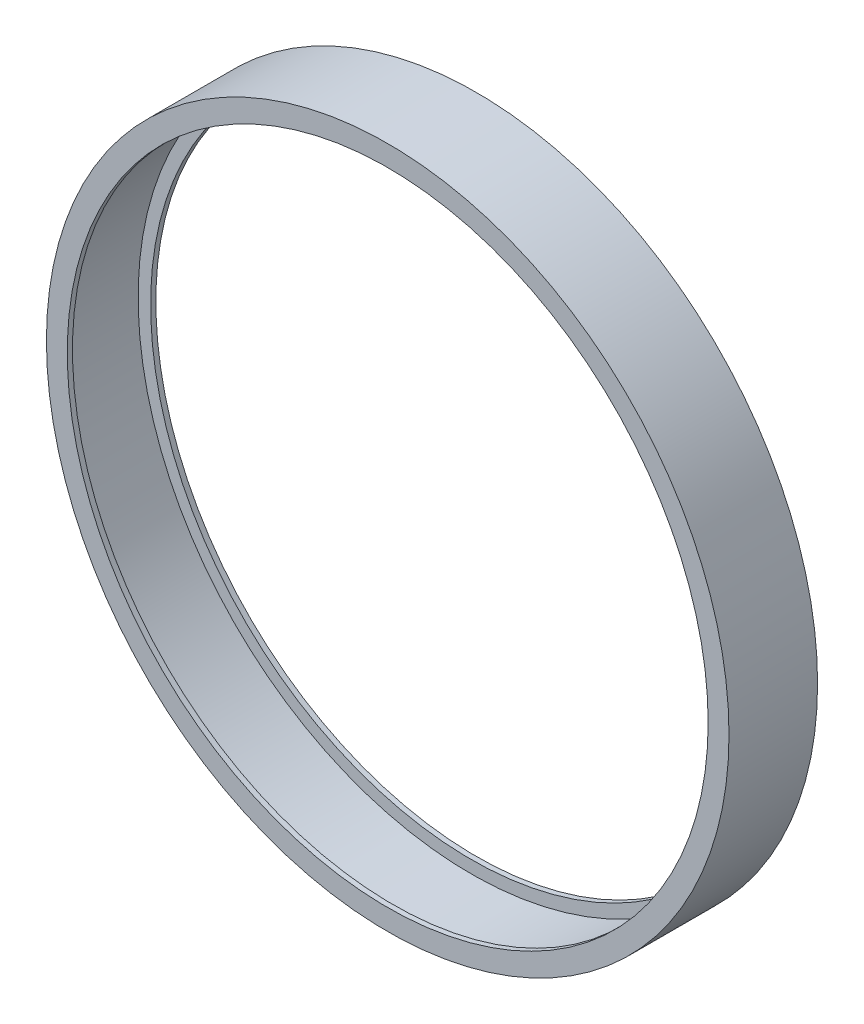
SolidWorks part; units mm, degrees
ref_plane "Front Plane" through (0, 0, 0) normal (0, 0, 1) x (1, 0, 0)
ref_plane "Top Plane" through (0, 0, 0) normal (0, 1, 0) x (1, 0, 0)
ref_plane "Right Plane" through (0, 0, 0) normal (1, 0, 0) x (0, 0, -1)
sketch "Sketch4" plane through (0, 0, 0) normal (1, 0, 0) x (0, 0, -1)
  line L0 (0, 0) -> (8.5, 0)
  line L1 (0, 0) -> (0, -2)
  line L2 (8.5, 0) -> (8.5, -2)
  line L3 (0, -2) -> (0.5, -2)
  line L4 (0.5, -2) -> (0.5, -0.8)
  line L5 (8.5, -2) -> (8, -2)
  line L6 (8, -2) -> (8, -0.8)
  line L7 (8, -0.8) -> (0.5, -0.8)
  line L8 (-15.4683, -32.75) -> (31.0944, -32.75) construction
  dimension "D1" = 2
  dimension "D2" = 2
  dimension "D3" = 8.5
  dimension "D4" = 0.5
  dimension "D5" = 0.5
  dimension "D6" = 32.75
revolve "Revolve1" add sketch "Sketch4" angle 360 about L8
